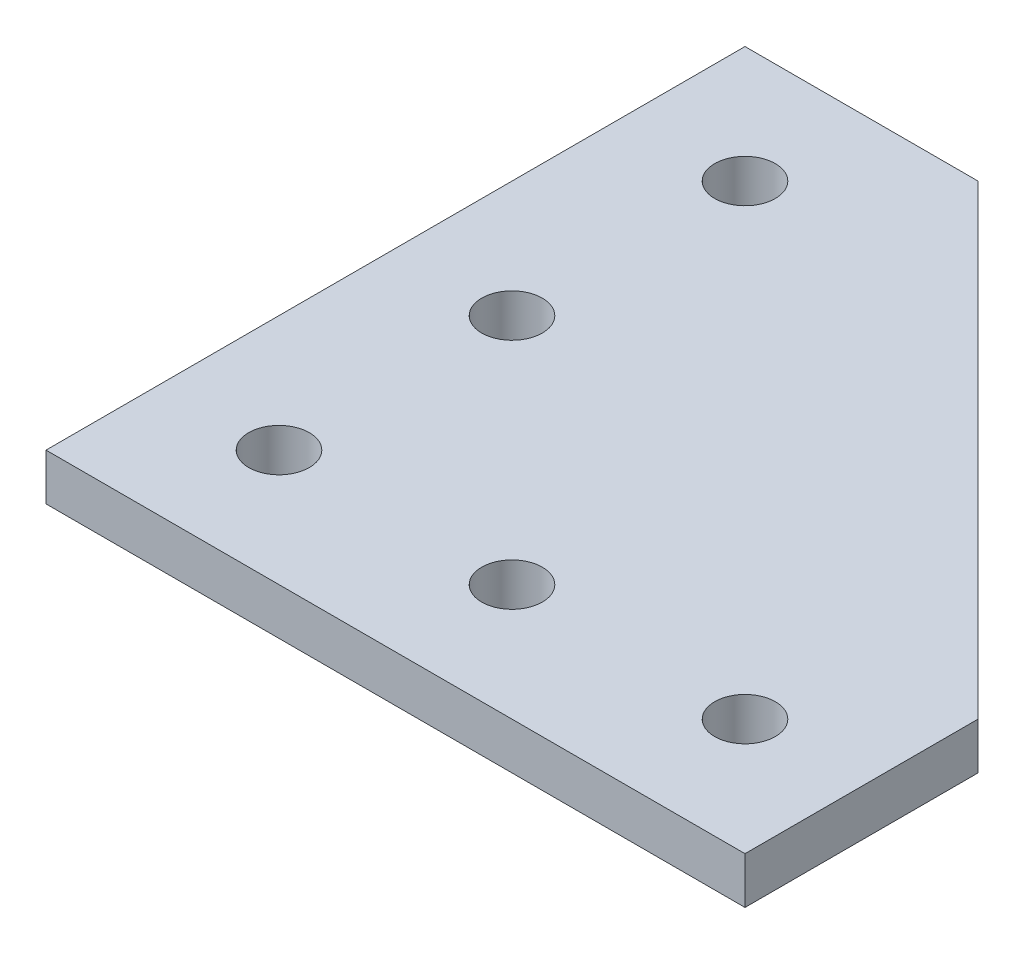
SolidWorks part; units mm, degrees
ref_plane "Front Plane" through (0, 0, 0) normal (0, 0, 1) x (1, 0, 0)
ref_plane "Top Plane" through (0, 0, 0) normal (0, 1, 0) x (1, 0, 0)
ref_plane "Right Plane" through (0, 0, 0) normal (1, 0, 0) x (0, 0, -1)
sketch "Sketch1" plane through (0, 0, 0) normal (0, 1, 0) x (1, 0, 0)
  line L0 (0, 0) -> (60, 0)
  line L1 (60, 0) -> (60, 20)
  line L2 (60, 20) -> (20, 60)
  line L3 (20, 60) -> (0, 60)
  line L4 (0, 60) -> (0, 0)
  line L5 (10, 60) -> (10, 0) construction
  line L6 (60, 10) -> (0, 10) construction
  circle A0 centre (10, 10) radius 2.6
  circle A1 centre (30, 10) radius 2.6
  circle A2 centre (50, 10) radius 2.6
  circle A3 centre (10, 30) radius 2.6
  circle A4 centre (10, 50) radius 2.6
  dimension "D3" = 5.2
  dimension "D1" = 20
  dimension "D2" = 60
  dimension "D4" = 20
  dimension "D5" = 20
extrude "Boss-Extrude1" add sketch "Sketch1" along normal blind 4
